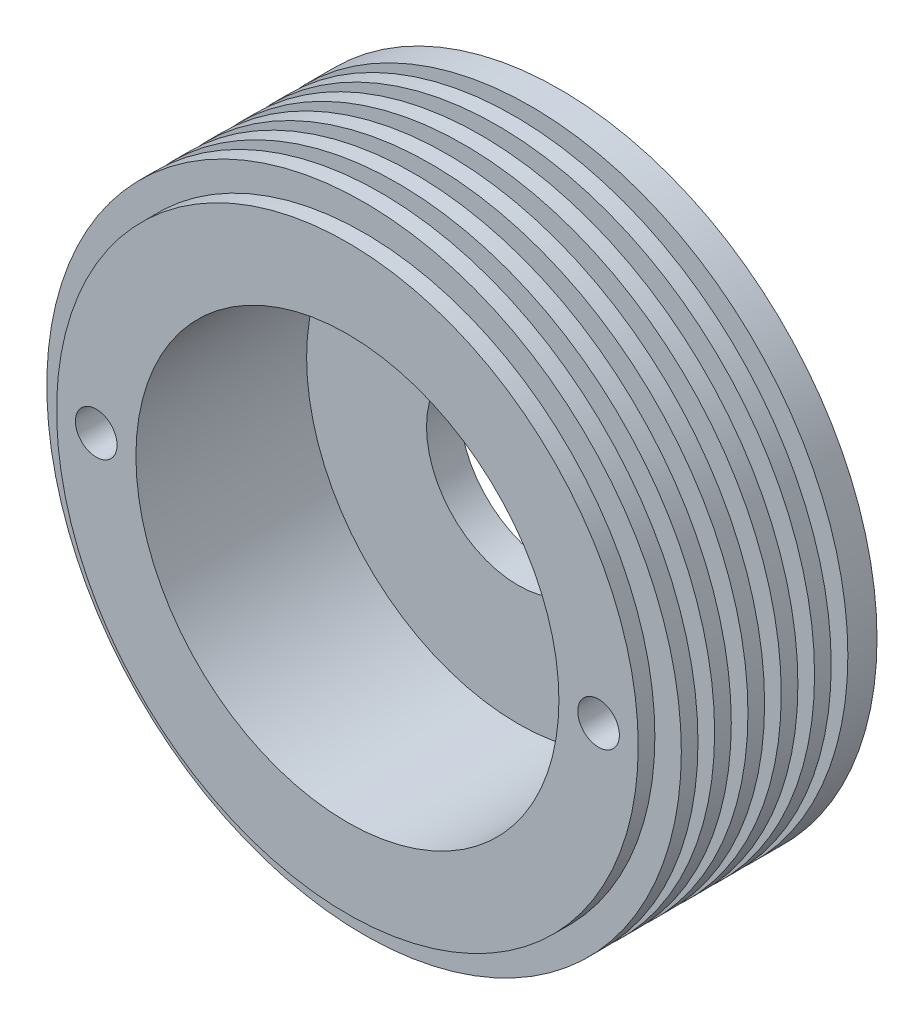
SolidWorks part; units mm, degrees
material "Alliage 1060"
ref_plane "Plan de face" through (0, 0, 0) normal (0, 0, 1) x (1, 0, 0)
ref_plane "Plan de dessus" through (0, 0, 0) normal (0, 1, 0) x (1, 0, 0)
ref_plane "Plan de droite" through (0, 0, 0) normal (1, 0, 0) x (0, 0, -1)
sketch "Esquisse1" plane through (0, 0, 0) normal (0, 0, 1) x (1, 0, 0)
  circle A0 centre (23.6795, 29.6707) radius 38.1
  dimension "D1" = 76.2
extrude "Boss.-Extru.1" add sketch "Esquisse1" along normal blind 25.5 contours A0
sketch "Esquisse3" plane through (0, 0, 25.5) normal (0, 0, 1) x (1, 0, 0)
  circle A0 centre (23.6795, 29.6707) radius 25.4
  dimension "D1" = 50.8
extrude "Enlèv. mat.-Extru.2" cut sketch "Esquisse3" against normal offset from surface (20.5 mm away) 5 up to face at (61.7795, 29.6707, 0)
sketch "Esquisse5" plane through (0, 0, 0) normal (0, 0, -1) x (-1, 0, 0)
  line L0 (-23.6795, 67.7707) -> (-23.6795, -8.4293) construction
  circle A0 centre (-23.6795, 29.6707) radius 11
  circle A1 centre (-23.6795, 29.6707) radius 38.1 construction
  point P7 (-23.6795, 29.6707)
  dimension "D1" = 22
extrude "Enlèv. mat.-Extru.3" cut sketch "Esquisse5" against normal up to surface (5 mm away) contours A0 up to face at (49.0795, 29.6707, 5)
sketch "Esquisse7" plane through (0, 0, 0) normal (0, 0, -1) x (-1, 0, 0)
  line L0 (-23.6795, 67.7707) -> (-23.6795, -8.4293) construction
  circle A1 centre (-23.6795, 29.6707) radius 38.1 construction
  circle A2 centre (-23.6795, 29.6707) radius 12.7
  dimension "D1" = 25.4
extrude "Enlèv. mat.-Extru.4" cut sketch "Esquisse7" against normal blind 1
sketch "Esquisse8" plane through (0, 0, 25.5) normal (0, 0, 1) x (1, 0, 0)
  circle A0 centre (23.6795, 29.6707) radius 34.925
  circle A1 centre (23.6795, 29.6707) radius 38.1
  dimension "D1" = 3.175
extrude "Enlèv. mat.-Extru.5" cut sketch "Esquisse8" against normal blind 2
pattern_linear "Répétition linéaire1" count 6 spacing 4 along (0, 0, -1) of "Enlèv. mat.-Extru.5"
sketch "Esquisse9" plane through (0, 0, 0) normal (0, 0, -1) x (-1, 0, 0)
  line L0 (-61.7795, 29.6707) -> (14.4205, 29.6707) construction
  circle A0 centre (6.483, 29.6707) radius 2.5
  circle A1 centre (-23.6795, 29.6707) radius 38.1 construction
  circle A2 centre (-53.842, 29.6707) radius 2.5
  point P7 (-23.6795, 29.6707)
  point P12 (-23.6795, 29.6707)
  dimension "D1" = 5
  dimension "D2" = 30.1625
  dimension "D3" = 2
extrude "Enlèv. mat.-Extru.6" cut sketch "Esquisse9" against normal through all
